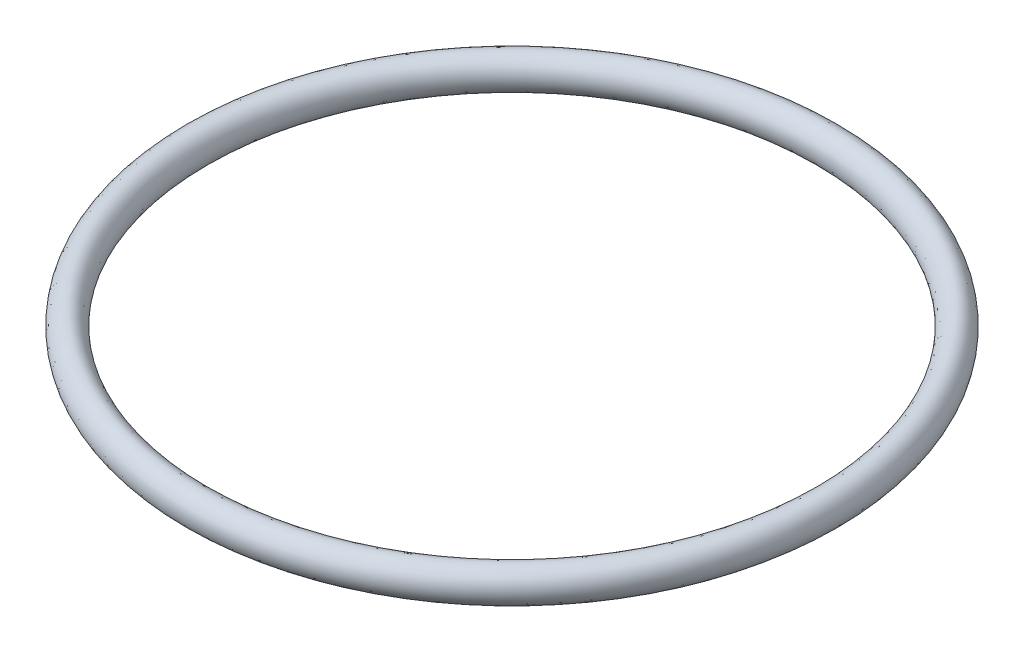
SolidWorks part; units mm, degrees
ref_plane "Front Plane" through (0, 0, 0) normal (0, 0, 1) x (1, 0, 0)
ref_plane "Top Plane" through (0, 0, 0) normal (0, 1, 0) x (1, 0, 0)
ref_plane "Right Plane" through (0, 0, 0) normal (1, 0, 0) x (0, 0, -1)
sketch "Sketch1" plane through (0, 0, 0) normal (0, 0, 1) x (1, 0, 0)
  line L0 (0, 0) -> (-33.45, 0)
  line L1 (-33.45, 0) -> (-35.15, 0)
  line L2 (0, 0) -> (0, 11.2268)
  ellipse E0 centre (-35.15, 0) end of major axis (-35.15, 1.9) minor radius 1.7
  dimension "D1" = 1.7
  dimension "D2" = 33.45
revolve "Revolve1" add sketch "Sketch1" angle 360 about L2
